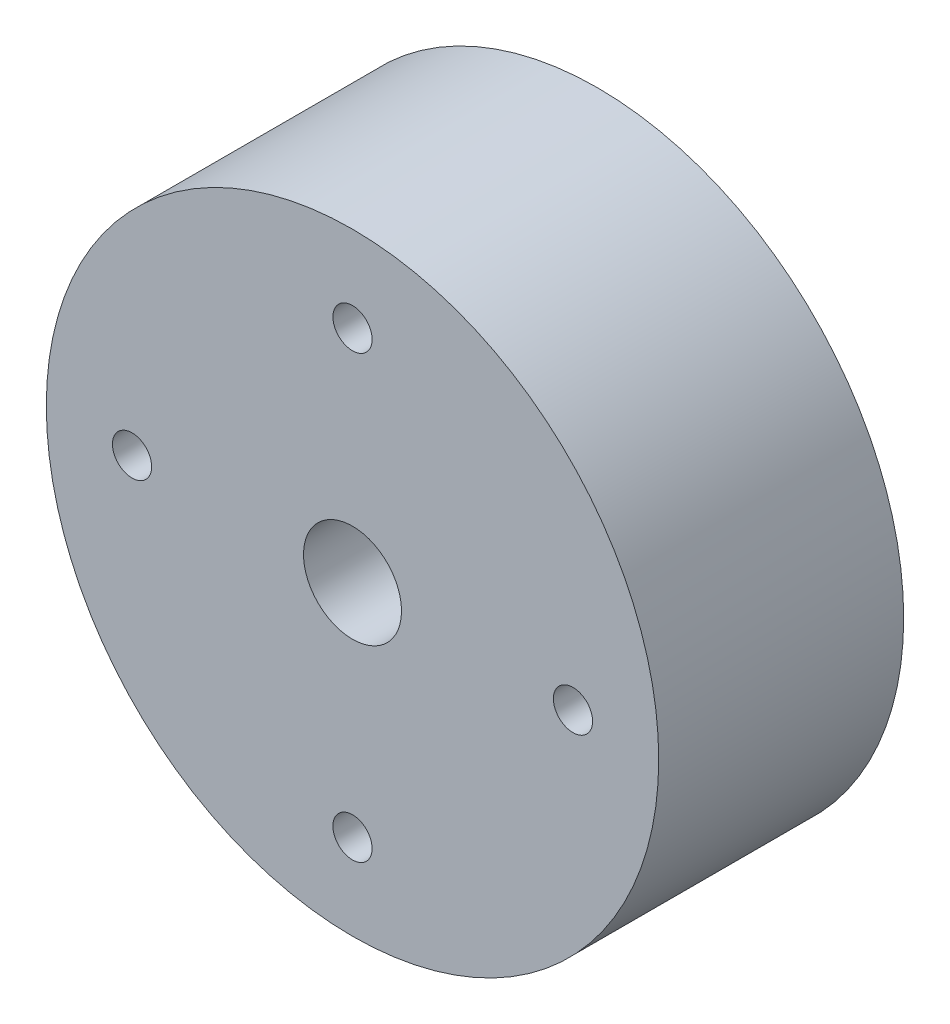
SolidWorks part; units mm, degrees
ref_plane "Front Plane" through (0, 0, 0) normal (0, 0, 1) x (1, 0, 0)
ref_plane "Top Plane" through (0, 0, 0) normal (0, 1, 0) x (1, 0, 0)
ref_plane "Right Plane" through (0, 0, 0) normal (1, 0, 0) x (0, 0, -1)
sketch "Sketch1" plane through (0, 0, 0) normal (0, 0, 1) x (1, 0, 0)
  line L0 (0, 0) -> (0, 18) construction
  circle A0 centre (0, 0) radius 25
  circle A1 centre (0, 0) radius 4
  circle A2 centre (0, 18) radius 1.6 construction
  dimension "D1" = 50
  dimension "D2" = 8
  dimension "D4" = 3.2
  dimension "D3" = 18
extrude "Boss-Extrude2" add sketch "Sketch1" along normal blind 20 contours A1 | A0
sketch "Sketch2" plane through (0, 0, 20) normal (0, 0, 1) x (1, 0, 0)
  circle A0 centre (0, 18) radius 1.6 construction
  circle A1 centre (0, 18) radius 1.6
  circle A2 centre (18, 0) radius 1.6
  circle A3 centre (0, -18) radius 1.6
  circle A4 centre (-18, 0) radius 1.6
  dimension "D1" = 4
extrude "Cut-Extrude1" cut sketch "Sketch2" against normal blind 10
